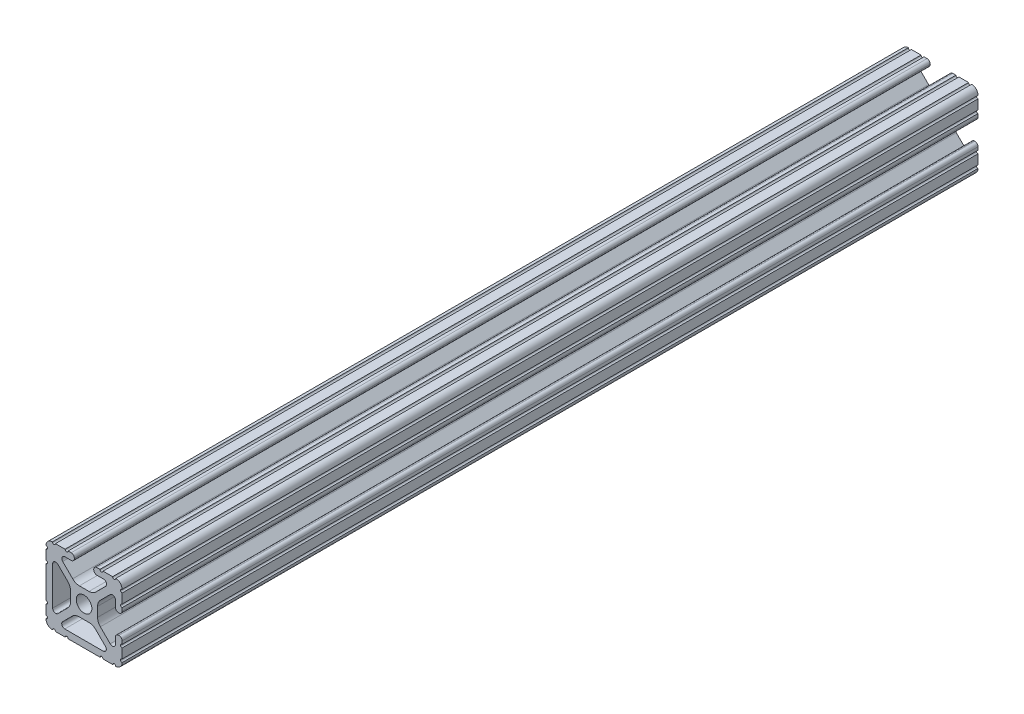
SolidWorks part; units mm, degrees
ref_plane "Front Plane" through (0, 0, 0) normal (0, 0, 1) x (1, 0, 0)
ref_plane "Top Plane" through (0, 0, 0) normal (0, 1, 0) x (1, 0, 0)
ref_plane "Right Plane" through (0, 0, 0) normal (1, 0, 0) x (0, 0, -1)
sketch "Sketch1" plane through (0, 0, 0) normal (0, 0, 1) x (1, 0, 0)
  line L0 (-3.2512, 12.7) -> (-3.2512, -12.7) construction
  line L1 (12.7, -12.7) -> (-12.7, -12.7)
  line L2 (12.7, -12.7) -> (12.7, 12.7)
  line L3 (12.7, 12.7) -> (-12.7, 12.7)
  line L4 (-12.7, -12.7) -> (-12.7, 12.7)
  line L5 (0, 12.7) -> (0, -12.7) construction
  line L6 (12.7, 0) -> (-12.7, 0) construction
  line L7 (-3.2512, -12.7) -> (3.2512, 12.7) construction
  line L8 (3.2512, 12.7) -> (3.2512, -12.7) construction
  circle A0 centre (0, 0) radius 2.6035
  point P0 (0, 0)
  line B0 (-10.4902, 6.4021) -> (-10.4902, -6.4254)
  line B1 (-5.4405, 3.8388) -> (-8.737, 7.1292)
  line B2 (-4.5085, -1.5917) -> (-4.5085, 1.5917)
  line B3 (-8.7534, -7.1457) -> (-5.4405, -3.8388)
  line B4 (-6.436, -10.4062) -> (6.4276, -10.4062)
  line B5 (-3.9003, -5.4237) -> (-7.1537, -8.6712)
  line B6 (1.6573, -4.4958) -> (-1.6573, -4.4958)
  line B7 (7.1478, -8.6653) -> (3.9003, -5.4237)
  line B8 (-5.3171, -12.7) -> (5.3171, -12.7)
  line B9 (6.3331, -12.7) -> (9.5504, -12.7)
  line B10 (12.7, -9.5504) -> (12.7, -6.3331)
  line B11 (12.7, -5.3171) -> (12.7, -4.2875)
  line B12 (11.651, -3.2385) -> (11.5392, -3.2385)
  line B13 (10.4902, -4.2875) -> (10.4902, -6.4021)
  line B14 (8.737, -7.1292) -> (5.4405, -3.8388)
  line B15 (4.5085, -1.5917) -> (4.5085, 1.5917)
  line B16 (5.4405, 3.8388) -> (8.737, 7.1292)
  line B17 (10.4902, 6.4021) -> (10.4902, 4.2875)
  line B18 (11.5392, 3.2385) -> (11.651, 3.2385)
  line B19 (12.7, 4.2875) -> (12.7, 5.3171)
  line B20 (12.7, 6.3331) -> (12.7, 9.5504)
  line B21 (9.5504, 12.7) -> (6.3331, 12.7)
  line B22 (5.3171, 12.7) -> (4.2875, 12.7)
  line B23 (3.2385, 11.651) -> (3.2385, 11.5392)
  line B24 (4.2875, 10.4902) -> (6.4768, 10.4902)
  line B25 (7.2072, 8.7246) -> (3.9003, 5.4237)
  line B26 (1.6573, 4.4958) -> (-1.5537, 4.4958)
  line B27 (-3.7967, 5.4237) -> (-7.1342, 8.7551)
  line B28 (-6.4164, 10.4902) -> (-4.2875, 10.4902)
  line B29 (-3.2385, 11.5392) -> (-3.2385, 11.651)
  line B30 (-4.2875, 12.7) -> (-5.3171, 12.7)
  line B31 (-6.3331, 12.7) -> (-9.5504, 12.7)
  line B32 (-12.7, 9.5504) -> (-12.7, 6.3331)
  line B33 (-12.7, 5.3171) -> (-12.7, -5.3171)
  line B34 (-12.7, -6.3331) -> (-12.7, -9.5504)
  line B35 (-9.5504, -12.7) -> (-6.3331, -12.7)
  circle B36 centre (0, 0) radius 2.6035
  arc B37 (-10.4902, -6.4254) -> (-8.7534, -7.1457) centre (-9.4724, -6.4254) ccw
  arc B38 (-8.737, 7.1292) -> (-10.4902, 6.4021) centre (-9.4628, 6.4021) ccw
  arc B39 (-4.5085, 1.5917) -> (-5.4405, 3.8388) centre (-7.6835, 1.5917) ccw
  arc B40 (-5.4405, -3.8388) -> (-4.5085, -1.5917) centre (-7.6835, -1.5917) ccw
  arc B41 (6.4276, -10.4062) -> (7.1478, -8.6653) centre (6.4276, -9.3868) ccw
  arc B42 (-7.1537, -8.6712) -> (-6.436, -10.4062) centre (-6.436, -9.3902) ccw
  arc B43 (-1.6573, -4.4958) -> (-3.9003, -5.4237) centre (-1.6573, -7.6708) ccw
  arc B44 (3.9003, -5.4237) -> (1.6573, -4.4958) centre (1.6573, -7.6708) ccw
  arc B45 (-5.3171, -12.7) -> (-6.3331, -12.7) centre (-5.8251, -12.7) ccw
  arc B46 (6.3331, -12.7) -> (5.3171, -12.7) centre (5.8251, -12.7) ccw
  arc B47 (10.5664, -12.6998) -> (9.5504, -12.7) centre (10.0584, -12.7) ccw
  arc B48 (10.5664, -12.6998) -> (12.6998, -10.5664) centre (10.5918, -10.5918) ccw
  arc B49 (12.7, -9.5504) -> (12.6998, -10.5664) centre (12.7, -10.0584) ccw
  arc B50 (12.7, -5.3171) -> (12.7, -6.3331) centre (12.7, -5.8251) ccw
  arc B51 (12.7, -4.2875) -> (11.651, -3.2385) centre (11.651, -4.2875) ccw
  arc B52 (11.5392, -3.2385) -> (10.4902, -4.2875) centre (11.5392, -4.2875) ccw
  arc B53 (8.737, -7.1292) -> (10.4902, -6.4021) centre (9.4628, -6.4021) ccw
  arc B54 (4.5085, -1.5917) -> (5.4405, -3.8388) centre (7.6835, -1.5917) ccw
  arc B55 (5.4405, 3.8388) -> (4.5085, 1.5917) centre (7.6835, 1.5917) ccw
  arc B56 (10.4902, 6.4021) -> (8.737, 7.1292) centre (9.4628, 6.4021) ccw
  arc B57 (10.4902, 4.2875) -> (11.5392, 3.2385) centre (11.5392, 4.2875) ccw
  arc B58 (11.651, 3.2385) -> (12.7, 4.2875) centre (11.651, 4.2875) ccw
  arc B59 (12.7, 6.3331) -> (12.7, 5.3171) centre (12.7, 5.8251) ccw
  arc B60 (12.6998, 10.5664) -> (12.7, 9.5504) centre (12.7, 10.0584) ccw
  arc B61 (12.6998, 10.5664) -> (10.5664, 12.6998) centre (10.5918, 10.5918) ccw
  arc B62 (9.5504, 12.7) -> (10.5664, 12.6998) centre (10.0584, 12.7) ccw
  arc B63 (5.3171, 12.7) -> (6.3331, 12.7) centre (5.8251, 12.7) ccw
  arc B64 (4.2875, 12.7) -> (3.2385, 11.651) centre (4.2875, 11.651) ccw
  arc B65 (3.2385, 11.5392) -> (4.2875, 10.4902) centre (4.2875, 11.5392) ccw
  arc B66 (7.2072, 8.7246) -> (6.4768, 10.4902) centre (6.4768, 9.4563) ccw
  arc B67 (1.6573, 4.4958) -> (3.9003, 5.4237) centre (1.6573, 7.6708) ccw
  arc B68 (-3.7967, 5.4237) -> (-1.5537, 4.4958) centre (-1.5537, 7.6708) ccw
  arc B69 (-6.4164, 10.4902) -> (-7.1342, 8.7551) centre (-6.4164, 9.4742) ccw
  arc B70 (-4.2875, 10.4902) -> (-3.2385, 11.5392) centre (-4.2875, 11.5392) ccw
  arc B71 (-3.2385, 11.651) -> (-4.2875, 12.7) centre (-4.2875, 11.651) ccw
  arc B72 (-6.3331, 12.7) -> (-5.3171, 12.7) centre (-5.8251, 12.7) ccw
  arc B73 (-10.5664, 12.6998) -> (-9.5504, 12.7) centre (-10.0584, 12.7) ccw
  arc B74 (-10.5664, 12.6998) -> (-12.6998, 10.5664) centre (-10.5918, 10.5918) ccw
  arc B75 (-12.7, 9.5504) -> (-12.6998, 10.5664) centre (-12.7, 10.0584) ccw
  arc B76 (-12.7, 5.3171) -> (-12.7, 6.3331) centre (-12.7, 5.8251) ccw
  arc B77 (-12.7, -6.3331) -> (-12.7, -5.3171) centre (-12.7, -5.8251) ccw
  arc B78 (-12.6998, -10.5664) -> (-12.7, -9.5504) centre (-12.7, -10.0584) ccw
  arc B79 (-12.6998, -10.5664) -> (-10.5664, -12.6998) centre (-10.5918, -10.5918) ccw
  arc B80 (-9.5504, -12.7) -> (-10.5664, -12.6998) centre (-10.0584, -12.7) ccw
  dimension "Center Hole Diameter" = 5.207
  dimension "Rail Width" = 25.4
  dimension "Rail Height" = 25.4
  dimension "T-Slot Width" = 6.5024
sketch_block_instance "Block1-1"
sketch_block "Block1"
sketch "Sketch2" plane through (0, 0, 0) normal (1, 0, 0) x (0, 0, -1)
  line L0 (-142.875, 0) -> (142.875, 0) construction
  line L1 (-142.875, 12.7) -> (-142.875, -12.7) construction
  line L2 (-142.875, -12.7) -> (142.875, -12.7) construction
  line L3 (142.875, -12.7) -> (142.875, 12.7) construction
  line L4 (-92.075, 0) -> (-92.075, 12.7) construction
  line L5 (-92.075, 12.7) -> (92.075, 12.7) construction
  line L6 (92.075, 12.7) -> (92.075, 0) construction
  line L7 (-142.875, -12.7) -> (142.875, -12.7)
  line L8 (-142.875, 12.7) -> (142.875, 12.7)
  point P7 (92.075, 0)
  point P11 (-92.075, 0)
  point P16 (0, -12.7)
  point P19 (0, 12.7)
  dimension "D1" = 50.8
  dimension "D2" = 50.8
  dimension "Rep Length" = 285.75
  dimension "Length Range [Max]" = 285.75
  dimension "Length Range [Min]" = 285.75
sketch "Sketch3" plane through (0, 0, 0) normal (0, 0, 1) x (1, 0, 0)
  line L0 (6.3331, -12.7) -> (9.5504, -12.7) construction
  line L1 (12.7, -9.5504) -> (12.7, -6.3331) construction
  line L2 (12.7, -5.3171) -> (12.7, -4.2875) construction
  line L3 (11.651, -3.2385) -> (11.5392, -3.2385) construction
  line L12 (10.4902, -4.2875) -> (10.4902, -6.4021) construction
  line L13 (8.737, -7.1292) -> (5.4405, -3.8388) construction
  line L14 (4.5085, -1.5917) -> (4.5085, 1.5917) construction
  line L15 (5.4405, 3.8388) -> (8.737, 7.1292) construction
  line L16 (10.4902, 6.4021) -> (10.4902, 4.2875) construction
  line L17 (11.5392, 3.2385) -> (11.651, 3.2385) construction
  line L18 (12.7, 4.2875) -> (12.7, 5.3171) construction
  line L19 (12.7, 6.3331) -> (12.7, 9.5504) construction
  line L20 (9.5504, 12.7) -> (6.3331, 12.7) construction
  line L21 (5.3171, 12.7) -> (4.2875, 12.7) construction
  line L22 (3.2385, 11.651) -> (3.2385, 11.5392) construction
  line L23 (4.2875, 10.4902) -> (6.4768, 10.4902) construction
  line L24 (7.2072, 8.7246) -> (3.9003, 5.4237) construction
  line L25 (1.6573, 4.4958) -> (-1.5537, 4.4958) construction
  line L26 (-3.7967, 5.4237) -> (-7.1342, 8.7551) construction
  line L27 (-6.4164, 10.4902) -> (-4.2875, 10.4902) construction
  line L28 (-3.2385, 11.5392) -> (-3.2385, 11.651) construction
  line L29 (-4.2875, 12.7) -> (-5.3171, 12.7) construction
  line L30 (-6.3331, 12.7) -> (-9.5504, 12.7) construction
  line L31 (-12.7, 9.5504) -> (-12.7, 6.3331) construction
  line L32 (-12.7, 5.3171) -> (-12.7, -5.3171) construction
  line L33 (-12.7, -6.3331) -> (-12.7, -9.5504) construction
  line L34 (-9.5504, -12.7) -> (-6.3331, -12.7) construction
  line L35 (-5.3171, -12.7) -> (5.3171, -12.7) construction
  line L36 (-8.7534, -7.1457) -> (-5.4405, -3.8388) construction
  line L37 (-10.4902, 6.4021) -> (-10.4902, -6.4254) construction
  line L38 (-5.4405, 3.8388) -> (-8.737, 7.1292) construction
  line L39 (-4.5085, -1.5917) -> (-4.5085, 1.5917) construction
  line L40 (7.1478, -8.6653) -> (3.9003, -5.4237) construction
  line L41 (-6.436, -10.4062) -> (6.4276, -10.4062) construction
  line L42 (-3.9003, -5.4237) -> (-7.1537, -8.6712) construction
  line L43 (1.6573, -4.4958) -> (-1.6573, -4.4958) construction
  line L44 (6.3331, -12.7) -> (9.5504, -12.7)
  line L45 (12.7, -9.5504) -> (12.7, -6.3331)
  line L46 (12.7, -5.3171) -> (12.7, -4.2875)
  line L47 (11.651, -3.2385) -> (11.5392, -3.2385)
  line L48 (10.4902, -4.2875) -> (10.4902, -6.4021)
  line L49 (8.737, -7.1292) -> (5.4405, -3.8388)
  line L50 (4.5085, -1.5917) -> (4.5085, 1.5917)
  line L51 (5.4405, 3.8388) -> (8.737, 7.1292)
  line L52 (10.4902, 6.4021) -> (10.4902, 4.2875)
  line L53 (11.5392, 3.2385) -> (11.651, 3.2385)
  line L54 (12.7, 4.2875) -> (12.7, 5.3171)
  line L55 (12.7, 6.3331) -> (12.7, 9.5504)
  line L56 (9.5504, 12.7) -> (6.3331, 12.7)
  line L57 (5.3171, 12.7) -> (4.2875, 12.7)
  line L58 (3.2385, 11.651) -> (3.2385, 11.5392)
  line L59 (4.2875, 10.4902) -> (6.4768, 10.4902)
  line L60 (7.2072, 8.7246) -> (3.9003, 5.4237)
  line L61 (1.6573, 4.4958) -> (-1.5537, 4.4958)
  line L62 (-3.7967, 5.4237) -> (-7.1342, 8.7551)
  line L63 (-6.4164, 10.4902) -> (-4.2875, 10.4902)
  line L64 (-3.2385, 11.5392) -> (-3.2385, 11.651)
  line L65 (-4.2875, 12.7) -> (-5.3171, 12.7)
  line L66 (-6.3331, 12.7) -> (-9.5504, 12.7)
  line L67 (-12.7, 9.5504) -> (-12.7, 6.3331)
  line L68 (-12.7, 5.3171) -> (-12.7, -5.3171)
  line L69 (-12.7, -6.3331) -> (-12.7, -9.5504)
  line L70 (-9.5504, -12.7) -> (-6.3331, -12.7)
  line L71 (-5.3171, -12.7) -> (5.3171, -12.7)
  line L72 (-8.7534, -7.1457) -> (-5.4405, -3.8388)
  line L73 (-10.4902, 6.4021) -> (-10.4902, -6.4254)
  line L74 (-5.4405, 3.8388) -> (-8.737, 7.1292)
  line L75 (-4.5085, -1.5917) -> (-4.5085, 1.5917)
  line L76 (7.1478, -8.6653) -> (3.9003, -5.4237)
  line L77 (-6.436, -10.4062) -> (6.4276, -10.4062)
  line L78 (-3.9003, -5.4237) -> (-7.1537, -8.6712)
  line L79 (1.6573, -4.4958) -> (-1.6573, -4.4958)
  arc A0 (10.5664, -12.6998) -> (9.5504, -12.7) centre (10.0584, -12.7) ccw construction
  circle A1 centre (0, 0) radius 2.6035
  circle A2 centre (0, 0) radius 2.6035
  arc A3 (10.5664, -12.6998) -> (12.6998, -10.5664) centre (10.5918, -10.5918) ccw construction
  arc A4 (12.7, -9.5504) -> (12.6998, -10.5664) centre (12.7, -10.0584) ccw construction
  arc A5 (12.7, -5.3171) -> (12.7, -6.3331) centre (12.7, -5.8251) ccw construction
  arc A6 (12.7, -4.2875) -> (11.651, -3.2385) centre (11.651, -4.2875) ccw construction
  arc A7 (11.5392, -3.2385) -> (10.4902, -4.2875) centre (11.5392, -4.2875) ccw construction
  arc A8 (8.737, -7.1292) -> (10.4902, -6.4021) centre (9.4628, -6.4021) ccw construction
  arc A9 (4.5085, -1.5917) -> (5.4405, -3.8388) centre (7.6835, -1.5917) ccw construction
  arc A10 (5.4405, 3.8388) -> (4.5085, 1.5917) centre (7.6835, 1.5917) ccw construction
  arc A11 (10.4902, 6.4021) -> (8.737, 7.1292) centre (9.4628, 6.4021) ccw construction
  arc A12 (10.4902, 4.2875) -> (11.5392, 3.2385) centre (11.5392, 4.2875) ccw construction
  arc A13 (11.651, 3.2385) -> (12.7, 4.2875) centre (11.651, 4.2875) ccw construction
  arc A14 (12.7, 6.3331) -> (12.7, 5.3171) centre (12.7, 5.8251) ccw construction
  arc A15 (12.6998, 10.5664) -> (12.7, 9.5504) centre (12.7, 10.0584) ccw construction
  arc A16 (12.6998, 10.5664) -> (10.5664, 12.6998) centre (10.5918, 10.5918) ccw construction
  arc A17 (9.5504, 12.7) -> (10.5664, 12.6998) centre (10.0584, 12.7) ccw construction
  arc A18 (5.3171, 12.7) -> (6.3331, 12.7) centre (5.8251, 12.7) ccw construction
  arc A19 (4.2875, 12.7) -> (3.2385, 11.651) centre (4.2875, 11.651) ccw construction
  arc A20 (3.2385, 11.5392) -> (4.2875, 10.4902) centre (4.2875, 11.5392) ccw construction
  arc A21 (7.2072, 8.7246) -> (6.4768, 10.4902) centre (6.4768, 9.4563) ccw construction
  arc A22 (1.6573, 4.4958) -> (3.9003, 5.4237) centre (1.6573, 7.6708) ccw construction
  arc A23 (-3.7967, 5.4237) -> (-1.5537, 4.4958) centre (-1.5537, 7.6708) ccw construction
  arc A24 (-6.4164, 10.4902) -> (-7.1342, 8.7551) centre (-6.4164, 9.4742) ccw construction
  arc A25 (-4.2875, 10.4902) -> (-3.2385, 11.5392) centre (-4.2875, 11.5392) ccw construction
  arc A26 (-3.2385, 11.651) -> (-4.2875, 12.7) centre (-4.2875, 11.651) ccw construction
  arc A27 (-6.3331, 12.7) -> (-5.3171, 12.7) centre (-5.8251, 12.7) ccw construction
  arc A28 (-10.5664, 12.6998) -> (-9.5504, 12.7) centre (-10.0584, 12.7) ccw construction
  arc A29 (-10.5664, 12.6998) -> (-12.6998, 10.5664) centre (-10.5918, 10.5918) ccw construction
  arc A30 (-12.7, 9.5504) -> (-12.6998, 10.5664) centre (-12.7, 10.0584) ccw construction
  arc A31 (-12.7, 5.3171) -> (-12.7, 6.3331) centre (-12.7, 5.8251) ccw construction
  arc A32 (-12.7, -6.3331) -> (-12.7, -5.3171) centre (-12.7, -5.8251) ccw construction
  arc A33 (-12.6998, -10.5664) -> (-12.7, -9.5504) centre (-12.7, -10.0584) ccw construction
  arc A34 (-12.6998, -10.5664) -> (-10.5664, -12.6998) centre (-10.5918, -10.5918) ccw construction
  arc A35 (-9.5504, -12.7) -> (-10.5664, -12.6998) centre (-10.0584, -12.7) ccw construction
  arc A36 (-5.3171, -12.7) -> (-6.3331, -12.7) centre (-5.8251, -12.7) ccw construction
  arc A37 (6.3331, -12.7) -> (5.3171, -12.7) centre (5.8251, -12.7) ccw construction
  arc A38 (-10.4902, -6.4254) -> (-8.7534, -7.1457) centre (-9.4724, -6.4254) ccw construction
  arc A39 (-8.737, 7.1292) -> (-10.4902, 6.4021) centre (-9.4628, 6.4021) ccw construction
  arc A40 (-4.5085, 1.5917) -> (-5.4405, 3.8388) centre (-7.6835, 1.5917) ccw construction
  arc A41 (-5.4405, -3.8388) -> (-4.5085, -1.5917) centre (-7.6835, -1.5917) ccw construction
  circle A42 centre (0, 0) radius 2.6035 construction
  arc A43 (6.4276, -10.4062) -> (7.1478, -8.6653) centre (6.4276, -9.3868) ccw construction
  arc A44 (-7.1537, -8.6712) -> (-6.436, -10.4062) centre (-6.436, -9.3902) ccw construction
  arc A45 (-1.6573, -4.4958) -> (-3.9003, -5.4237) centre (-1.6573, -7.6708) ccw construction
  arc A46 (3.9003, -5.4237) -> (1.6573, -4.4958) centre (1.6573, -7.6708) ccw construction
  arc A47 (10.5664, -12.6998) -> (9.5504, -12.7) centre (10.0584, -12.7) ccw
  arc A48 (10.5664, -12.6998) -> (12.6998, -10.5664) centre (10.5918, -10.5918) ccw
  arc A49 (12.7, -9.5504) -> (12.6998, -10.5664) centre (12.7, -10.0584) ccw
  arc A50 (12.7, -5.3171) -> (12.7, -6.3331) centre (12.7, -5.8251) ccw
  arc A51 (12.7, -4.2875) -> (11.651, -3.2385) centre (11.651, -4.2875) ccw
  arc A52 (11.5392, -3.2385) -> (10.4902, -4.2875) centre (11.5392, -4.2875) ccw
  arc A53 (8.737, -7.1292) -> (10.4902, -6.4021) centre (9.4628, -6.4021) ccw
  arc A54 (4.5085, -1.5917) -> (5.4405, -3.8388) centre (7.6835, -1.5917) ccw
  arc A55 (5.4405, 3.8388) -> (4.5085, 1.5917) centre (7.6835, 1.5917) ccw
  arc A56 (10.4902, 6.4021) -> (8.737, 7.1292) centre (9.4628, 6.4021) ccw
  arc A57 (10.4902, 4.2875) -> (11.5392, 3.2385) centre (11.5392, 4.2875) ccw
  arc A58 (11.651, 3.2385) -> (12.7, 4.2875) centre (11.651, 4.2875) ccw
  arc A59 (12.7, 6.3331) -> (12.7, 5.3171) centre (12.7, 5.8251) ccw
  arc A60 (12.6998, 10.5664) -> (12.7, 9.5504) centre (12.7, 10.0584) ccw
  arc A61 (12.6998, 10.5664) -> (10.5664, 12.6998) centre (10.5918, 10.5918) ccw
  arc A62 (9.5504, 12.7) -> (10.5664, 12.6998) centre (10.0584, 12.7) ccw
  arc A63 (5.3171, 12.7) -> (6.3331, 12.7) centre (5.8251, 12.7) ccw
  arc A64 (4.2875, 12.7) -> (3.2385, 11.651) centre (4.2875, 11.651) ccw
  arc A65 (3.2385, 11.5392) -> (4.2875, 10.4902) centre (4.2875, 11.5392) ccw
  arc A66 (7.2072, 8.7246) -> (6.4768, 10.4902) centre (6.4768, 9.4563) ccw
  arc A67 (1.6573, 4.4958) -> (3.9003, 5.4237) centre (1.6573, 7.6708) ccw
  arc A68 (-3.7967, 5.4237) -> (-1.5537, 4.4958) centre (-1.5537, 7.6708) ccw
  arc A69 (-6.4164, 10.4902) -> (-7.1342, 8.7551) centre (-6.4164, 9.4742) ccw
  arc A70 (-4.2875, 10.4902) -> (-3.2385, 11.5392) centre (-4.2875, 11.5392) ccw
  arc A71 (-3.2385, 11.651) -> (-4.2875, 12.7) centre (-4.2875, 11.651) ccw
  arc A72 (-6.3331, 12.7) -> (-5.3171, 12.7) centre (-5.8251, 12.7) ccw
  arc A73 (-10.5664, 12.6998) -> (-9.5504, 12.7) centre (-10.0584, 12.7) ccw
  arc A74 (-10.5664, 12.6998) -> (-12.6998, 10.5664) centre (-10.5918, 10.5918) ccw
  arc A75 (-12.7, 9.5504) -> (-12.6998, 10.5664) centre (-12.7, 10.0584) ccw
  arc A76 (-12.7, 5.3171) -> (-12.7, 6.3331) centre (-12.7, 5.8251) ccw
  arc A77 (-12.7, -6.3331) -> (-12.7, -5.3171) centre (-12.7, -5.8251) ccw
  arc A78 (-12.6998, -10.5664) -> (-12.7, -9.5504) centre (-12.7, -10.0584) ccw
  arc A79 (-12.6998, -10.5664) -> (-10.5664, -12.6998) centre (-10.5918, -10.5918) ccw
  arc A80 (-9.5504, -12.7) -> (-10.5664, -12.6998) centre (-10.0584, -12.7) ccw
  arc A81 (-5.3171, -12.7) -> (-6.3331, -12.7) centre (-5.8251, -12.7) ccw
  arc A82 (6.3331, -12.7) -> (5.3171, -12.7) centre (5.8251, -12.7) ccw
  arc A83 (-10.4902, -6.4254) -> (-8.7534, -7.1457) centre (-9.4724, -6.4254) ccw
  arc A84 (-8.737, 7.1292) -> (-10.4902, 6.4021) centre (-9.4628, 6.4021) ccw
  arc A85 (-4.5085, 1.5917) -> (-5.4405, 3.8388) centre (-7.6835, 1.5917) ccw
  arc A86 (-5.4405, -3.8388) -> (-4.5085, -1.5917) centre (-7.6835, -1.5917) ccw
  circle A87 centre (0, 0) radius 2.6035
  arc A88 (6.4276, -10.4062) -> (7.1478, -8.6653) centre (6.4276, -9.3868) ccw
  arc A89 (-7.1537, -8.6712) -> (-6.436, -10.4062) centre (-6.436, -9.3902) ccw
  arc A90 (-1.6573, -4.4958) -> (-3.9003, -5.4237) centre (-1.6573, -7.6708) ccw
  arc A91 (3.9003, -5.4237) -> (1.6573, -4.4958) centre (1.6573, -7.6708) ccw
  dimension "D1" = 0
extrude "Boss-Extrude1" add sketch "Sketch3" along normal up to vertex (142.875 mm away) and the other way up to vertex (142.875 mm away) contours A82 L44 A47 A48 A49 L45 A50 L46 A51 L47 A52 L48 A53 L49 A54 L50 A55 L51 A56 L52 A57 L53 A58 L54 A59 L55 A60 A61 A62 L56 A63 L57 A64 L58 A65 L59 A66 L60 A67 L61 A68 L62 A69 L63 A70 L64 A71 L65 A72 L66 A73 up to point (0, 0, 142.875) other way up to point (0, 0, -142.875)
